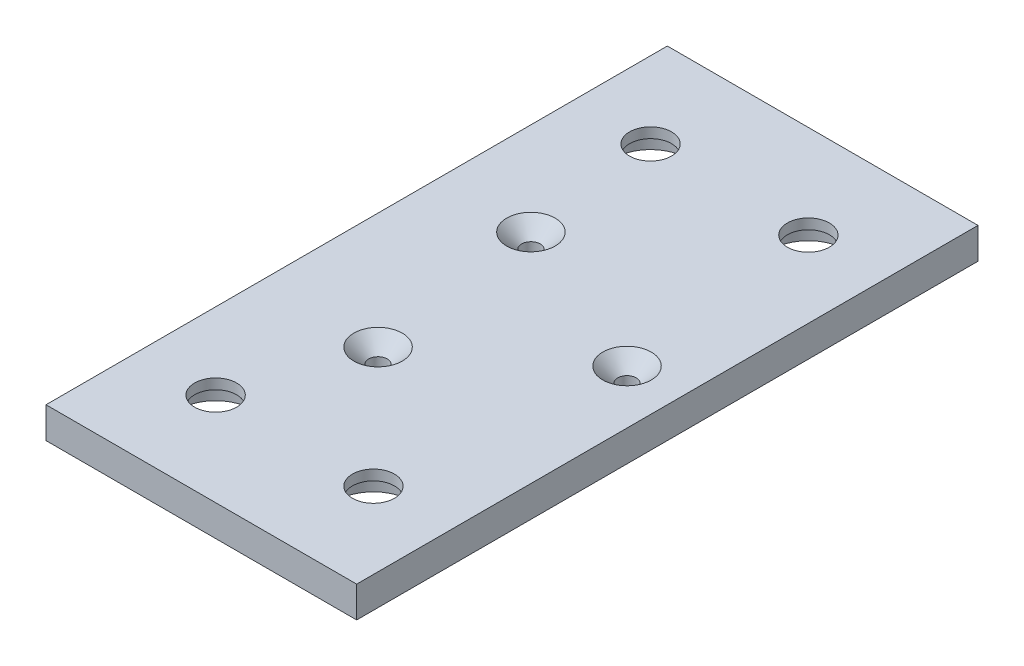
SolidWorks part; units mm, degrees
ref_plane "Front Plane" through (0, 0, 0) normal (0, 0, 1) x (1, 0, 0)
ref_plane "Top Plane" through (0, 0, 0) normal (0, 1, 0) x (1, 0, 0)
ref_plane "Right Plane" through (0, 0, 0) normal (1, 0, 0) x (0, 0, -1)
sketch "Sketch1" plane through (0, 0, 0) normal (0, 1, 0) x (1, 0, 0)
  line L1 (-25, -50) -> (25, -50)
  line L2 (-25, -50) -> (-25, 50)
  line L3 (-25, 50) -> (25, 50)
  line L4 (25, -50) -> (25, 50)
  line L5 (-25, -50) -> (25, 50) construction
  line L6 (-25, 50) -> (25, -50) construction
  point P0 (0, 0)
  dimension "D1" = 100
  dimension "D2" = 50
extrude "Boss-Extrude1" add sketch "Sketch1" along normal blind 5
sketch "Sketch3" plane through (0, 5, 0) normal (0, 1, 0) x (1, 0, 0)
  line L0 (0, 0) -> (0, -50) construction
  line L1 (-25, -50) -> (25, -50) construction
  line L2 (0, 0) -> (25, 0) construction
  line L3 (25, -50) -> (25, 50) construction
  line L4 (0, 0) -> (-20.7107, -50) construction
  line L5 (0, 0) -> (25, 3.2913) construction
  line L6 (0, 0) -> (-25, 32.5806) construction
  line L7 (-25, 50) -> (-25, -50) construction
  circle A0 centre (-6.3143, -15.244) radius 1.5
  circle A1 centre (16.3588, 2.1537) radius 1.5
  circle A2 centre (-10.0446, 13.0903) radius 1.5
  dimension "D2" = 3
  dimension "D5" = 3
  dimension "D8" = 3
  dimension "D1" = 22.5
  dimension "D3" = 16.5
  dimension "D4" = 120
  dimension "D6" = 16.5
  dimension "D7" = 120
  dimension "D9" = 16.5
extrude "Cut-Extrude2" cut sketch "Sketch3" against normal blind 5
sketch "Sketch4" plane through (0, 5, 0) normal (0, 1, 0) x (1, 0, 0)
  line L0 (0, 0) -> (95.9173, 0) construction
  line L1 (0, 0) -> (0, 78.6934) construction
  circle A0 centre (12.7, 35) radius 2.413
  circle A1 centre (-12.7, 35) radius 2.413
  circle A2 centre (12.7, -35) radius 2.413
  circle A3 centre (-12.7, -35) radius 2.413
  dimension "D1" = 4.826
  dimension "D2" = 35
  dimension "D3" = 12.7
chamfer "Chamfer1" distance 2.4 angle 45 3 edges at (-6.3143, 5, 16.744) (16.3588, 5, -0.6537) (-10.0446, 5, -11.5903)
hole_wizard "CBORE for 1/4 Button Head Cap Screw2" positions "Sketch10" profile "Sketch9" counterbore size "1/4" standard "ANSI Inch" end condition through all
sketch "Sketch10" plane through (0, 0, 0) normal (0, -1, 0) x (-1, 0, 0)
  point P0 (12.7, -35)
  point P3 (-12.7, -35)
  point P6 (-12.7, 35)
  point P9 (12.7, 35)
sketch "Sketch9" plane through (-12.7, 0, 35) normal (1, 0, 0) x (0, 0, -1)
  line L0 (0, 0) -> (0, 5)
  line L1 (0, 5) -> (3.3782, 5)
  line L3 (3.3782, 5) -> (3.3782, 3.3528)
  line L4 (3.3782, 3.3528) -> (5.9538, 3.3528)
  line L5 (5.9538, 3.3528) -> (5.9538, 0)
  line L7 (5.9538, 0) -> (0, 0)
  line L11 (0, -6.35) -> (0, 107.95) construction
  dimension "Thru Hole Dia." = 6.7564
  dimension "Thru Hole Depth" = 5
  dimension "C'Bore Dia." = 11.9075
  dimension "C'Bore Depth" = 3.3528
